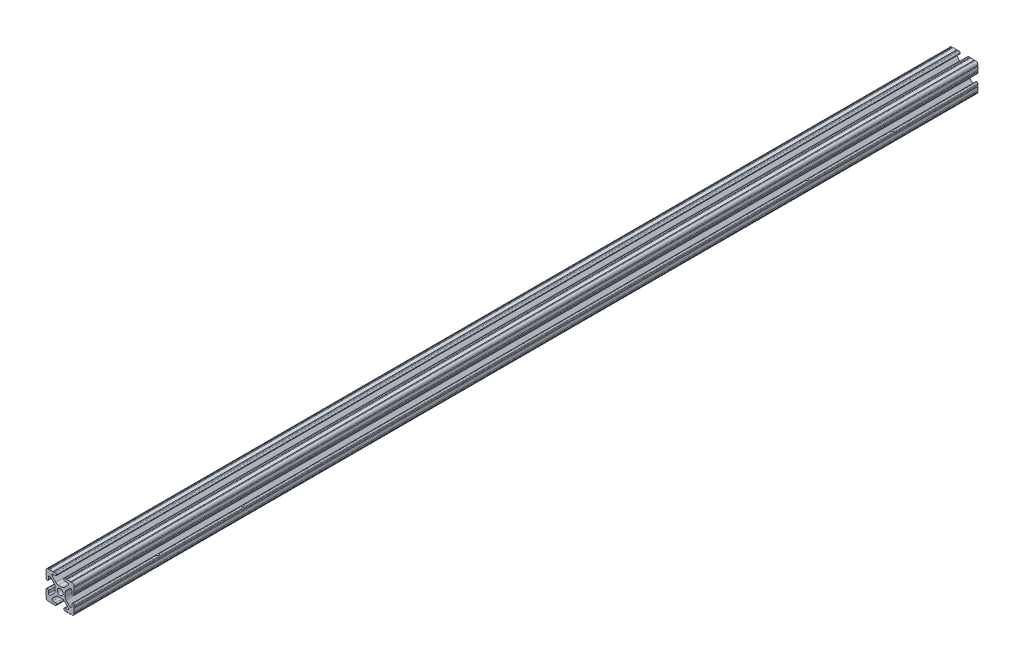
SolidWorks part; units mm, degrees
ref_plane "Front Plane" through (0, 0, 0) normal (0, 0, 1) x (1, 0, 0)
ref_plane "Top Plane" through (0, 0, 0) normal (0, 1, 0) x (1, 0, 0)
ref_plane "Right Plane" through (0, 0, 0) normal (1, 0, 0) x (0, 0, -1)
sketch "Sketch1" plane through (0, 0, 0) normal (0, 0, 1) x (1, 0, 0)
  line L88 (-7.1797, -8.6452) -> (-3.9523, -5.4237)
  line L89 (-1.7093, -4.4958) -> (1.7093, -4.4958)
  line L90 (3.9523, -5.4237) -> (7.1797, -8.6452)
  line L91 (6.4164, -10.4902) -> (4.2875, -10.4902)
  line L92 (3.2385, -11.5392) -> (3.2385, -11.651)
  line L93 (4.2875, -12.7) -> (5.3171, -12.7)
  line L94 (6.3331, -12.7) -> (9.5504, -12.7)
  line L95 (12.7, -9.5504) -> (12.7, -6.3331)
  line L96 (12.7, -5.3171) -> (12.7, -4.2875)
  line L97 (11.651, -3.2385) -> (11.5392, -3.2385)
  line L98 (10.4902, -4.2875) -> (10.4902, -6.4021)
  line L99 (8.7371, -7.1294) -> (5.441, -3.8408)
  line L100 (4.5085, -1.5932) -> (4.5085, 1.5932)
  line L101 (5.441, 3.8408) -> (8.7371, 7.1294)
  line L102 (10.4902, 6.4021) -> (10.4902, 4.2875)
  line L103 (11.5392, 3.2385) -> (11.651, 3.2385)
  line L104 (12.7, 4.2875) -> (12.7, 5.3171)
  line L105 (12.7, 6.3331) -> (12.7, 9.5504)
  line L106 (9.5504, 12.7) -> (6.3331, 12.7)
  line L107 (5.3171, 12.7) -> (4.2875, 12.7)
  line L108 (3.2385, 11.651) -> (3.2385, 11.5392)
  line L109 (4.2875, 10.4902) -> (6.4768, 10.4902)
  line L110 (7.207, 8.7244) -> (3.8983, 5.4232)
  line L111 (1.6558, 4.4958) -> (-1.6558, 4.4958)
  line L112 (-3.8983, 5.4232) -> (-7.207, 8.7244)
  line L113 (-6.4768, 10.4902) -> (-4.2875, 10.4902)
  line L114 (-3.2385, 11.5392) -> (-3.2385, 11.651)
  line L115 (-4.2875, 12.7) -> (-5.3171, 12.7)
  line L116 (-6.3331, 12.7) -> (-9.5504, 12.7)
  line L117 (-12.7, 9.5504) -> (-12.7, 6.3331)
  line L118 (-12.7, 5.3171) -> (-12.7, 4.2875)
  line L119 (-11.651, 3.2385) -> (-11.5392, 3.2385)
  line L120 (-10.4902, 4.2875) -> (-10.4902, 6.4021)
  line L121 (-8.7371, 7.1294) -> (-5.441, 3.8408)
  line L122 (-4.5085, 1.5932) -> (-4.5085, -1.5932)
  line L123 (-5.441, -3.8408) -> (-8.7371, -7.1294)
  line L124 (-10.4902, -6.4021) -> (-10.4902, -4.2875)
  line L125 (-11.5392, -3.2385) -> (-11.651, -3.2385)
  line L126 (-12.7, -4.2875) -> (-12.7, -5.3171)
  line L127 (-12.7, -6.3331) -> (-12.7, -9.5504)
  line L128 (-9.5504, -12.7) -> (-6.3331, -12.7)
  line L129 (-5.3171, -12.7) -> (-4.2875, -12.7)
  line L130 (-3.2385, -11.651) -> (-3.2385, -11.5392)
  line L131 (-4.2875, -10.4902) -> (-6.4164, -10.4902)
  circle A1 centre (0, 0) radius 2.6035
  arc A104 (-7.1797, -8.6452) -> (-6.4164, -10.4902) centre (-6.4164, -9.4098) ccw
  arc A105 (-1.7093, -4.4958) -> (-3.9523, -5.4237) centre (-1.7093, -7.6708) ccw
  arc A106 (3.9523, -5.4237) -> (1.7093, -4.4958) centre (1.7093, -7.6708) ccw
  arc A107 (6.4164, -10.4902) -> (7.1797, -8.6452) centre (6.4164, -9.4098) ccw
  arc A108 (4.2875, -10.4902) -> (3.2385, -11.5392) centre (4.2875, -11.5392) ccw
  arc A109 (3.2385, -11.651) -> (4.2875, -12.7) centre (4.2875, -11.651) ccw
  arc A110 (6.3331, -12.7) -> (5.3171, -12.7) centre (5.8251, -12.7) ccw
  arc A111 (10.5664, -12.6998) -> (9.5504, -12.7) centre (10.0584, -12.7) ccw
  arc A112 (10.5664, -12.6998) -> (12.6998, -10.5664) centre (10.5918, -10.5918) ccw
  arc A113 (12.7, -9.5504) -> (12.6998, -10.5664) centre (12.7, -10.0584) ccw
  arc A114 (12.7, -5.3171) -> (12.7, -6.3331) centre (12.7, -5.8251) ccw
  arc A115 (12.7, -4.2875) -> (11.651, -3.2385) centre (11.651, -4.2875) ccw
  arc A116 (11.5392, -3.2385) -> (10.4902, -4.2875) centre (11.5392, -4.2875) ccw
  arc A117 (8.7371, -7.1294) -> (10.4902, -6.4021) centre (9.4628, -6.4021) ccw
  arc A118 (4.5085, -1.5932) -> (5.441, -3.8408) centre (7.6835, -1.5932) ccw
  arc A119 (5.441, 3.8408) -> (4.5085, 1.5932) centre (7.6835, 1.5932) ccw
  arc A120 (10.4902, 6.4021) -> (8.7371, 7.1294) centre (9.4628, 6.4021) ccw
  arc A121 (10.4902, 4.2875) -> (11.5392, 3.2385) centre (11.5392, 4.2875) ccw
  arc A122 (11.651, 3.2385) -> (12.7, 4.2875) centre (11.651, 4.2875) ccw
  arc A123 (12.7, 6.3331) -> (12.7, 5.3171) centre (12.7, 5.8251) ccw
  arc A124 (12.6998, 10.5664) -> (12.7, 9.5504) centre (12.7, 10.0584) ccw
  arc A125 (12.6998, 10.5664) -> (10.5664, 12.6998) centre (10.5918, 10.5918) ccw
  arc A126 (9.5504, 12.7) -> (10.5664, 12.6998) centre (10.0584, 12.7) ccw
  arc A127 (5.3171, 12.7) -> (6.3331, 12.7) centre (5.8251, 12.7) ccw
  arc A128 (4.2875, 12.7) -> (3.2385, 11.651) centre (4.2875, 11.651) ccw
  arc A129 (3.2385, 11.5392) -> (4.2875, 10.4902) centre (4.2875, 11.5392) ccw
  arc A130 (7.207, 8.7244) -> (6.4768, 10.4902) centre (6.4768, 9.4563) ccw
  arc A131 (1.6558, 4.4958) -> (3.8983, 5.4232) centre (1.6558, 7.6708) ccw
  arc A132 (-3.8983, 5.4232) -> (-1.6558, 4.4958) centre (-1.6558, 7.6708) ccw
  arc A133 (-6.4768, 10.4902) -> (-7.207, 8.7244) centre (-6.4768, 9.4563) ccw
  arc A134 (-4.2875, 10.4902) -> (-3.2385, 11.5392) centre (-4.2875, 11.5392) ccw
  arc A135 (-3.2385, 11.651) -> (-4.2875, 12.7) centre (-4.2875, 11.651) ccw
  arc A136 (-6.3331, 12.7) -> (-5.3171, 12.7) centre (-5.8251, 12.7) ccw
  arc A137 (-10.5664, 12.6998) -> (-9.5504, 12.7) centre (-10.0584, 12.7) ccw
  arc A138 (-10.5664, 12.6998) -> (-12.6998, 10.5664) centre (-10.5918, 10.5918) ccw
  arc A139 (-12.7, 9.5504) -> (-12.6998, 10.5664) centre (-12.7, 10.0584) ccw
  arc A140 (-12.7, 5.3171) -> (-12.7, 6.3331) centre (-12.7, 5.8251) ccw
  arc A141 (-12.7, 4.2875) -> (-11.651, 3.2385) centre (-11.651, 4.2875) ccw
  arc A142 (-11.5392, 3.2385) -> (-10.4902, 4.2875) centre (-11.5392, 4.2875) ccw
  arc A143 (-8.7371, 7.1294) -> (-10.4902, 6.4021) centre (-9.4628, 6.4021) ccw
  arc A144 (-4.5085, 1.5932) -> (-5.441, 3.8408) centre (-7.6835, 1.5932) ccw
  arc A145 (-5.441, -3.8408) -> (-4.5085, -1.5932) centre (-7.6835, -1.5932) ccw
  arc A146 (-10.4902, -6.4021) -> (-8.7371, -7.1294) centre (-9.4628, -6.4021) ccw
  arc A147 (-10.4902, -4.2875) -> (-11.5392, -3.2385) centre (-11.5392, -4.2875) ccw
  arc A148 (-11.651, -3.2385) -> (-12.7, -4.2875) centre (-11.651, -4.2875) ccw
  arc A149 (-12.7, -6.3331) -> (-12.7, -5.3171) centre (-12.7, -5.8251) ccw
  arc A150 (-12.6998, -10.5664) -> (-12.7, -9.5504) centre (-12.7, -10.0584) ccw
  arc A151 (-12.6998, -10.5664) -> (-10.5664, -12.6998) centre (-10.5918, -10.5918) ccw
  arc A152 (-9.5504, -12.7) -> (-10.5664, -12.6998) centre (-10.0584, -12.7) ccw
  arc A153 (-5.3171, -12.7) -> (-6.3331, -12.7) centre (-5.8251, -12.7) ccw
  arc A154 (-4.2875, -12.7) -> (-3.2385, -11.651) centre (-4.2875, -11.651) ccw
  arc A155 (-3.2385, -11.5392) -> (-4.2875, -10.4902) centre (-4.2875, -11.5392) ccw
extrude "Boss-Extrude1" add sketch "Sketch1" along normal mid plane 812.8
sketch "Sketch3" plane through (4.5085, 0, 0) normal (1, 0, 0) x (0, 0, -1)
  line L0 (0, 0) -> (0, -131.3157) construction
  line L1 (406.4, -1.5932) -> (406.4, 1.5932) construction
  circle A0 centre (254, 0) radius 3.5
  circle A1 centre (-254, 0) radius 3.5
  circle A2 centre (330.2, 0) radius 3.5
  circle A3 centre (-330.2, 0) radius 3.5
  point P11 (0, 0)
  dimension "D1" = 7
  dimension "D3" = 7
  dimension "D4" = 76.2
  dimension "D2" = 152.4
extrude "Cut-Extrude2" cut sketch "Sketch3" against normal through all both and the other way through all
